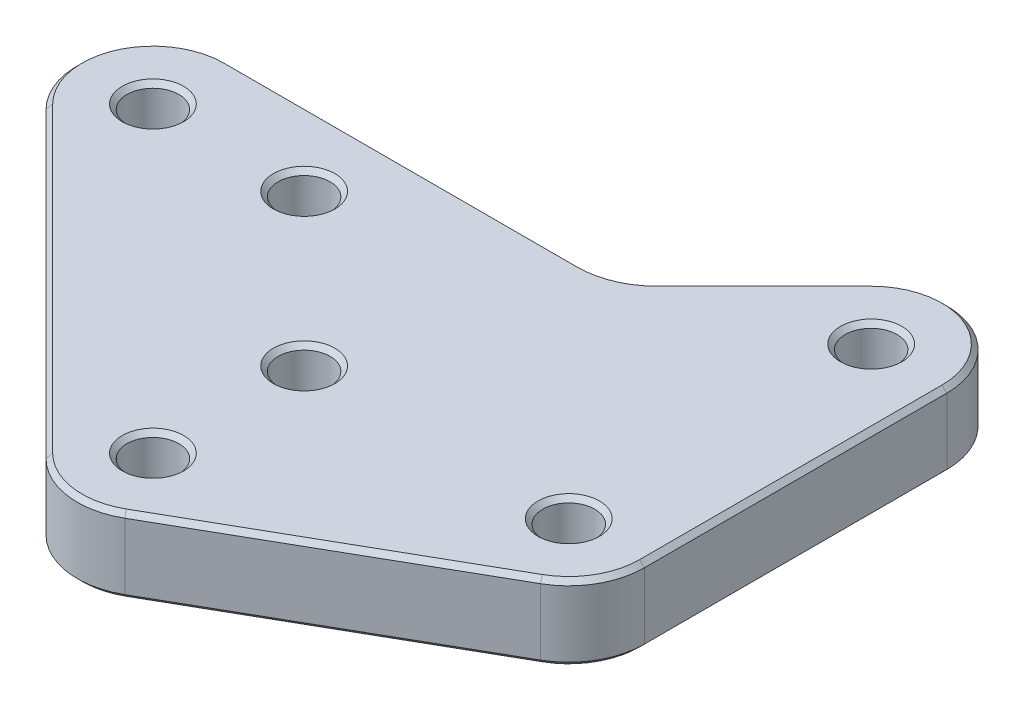
SolidWorks part; units mm, degrees
ref_plane "Front Plane" through (0, 0, 0) normal (0, 0, 1) x (1, 0, 0)
ref_plane "Top Plane" through (0, 0, 0) normal (0, 1, 0) x (1, 0, 0)
ref_plane "Right Plane" through (0, 0, 0) normal (1, 0, 0) x (0, 0, -1)
sketch "Sketch1" plane through (0, 0, 0) normal (0, 1, 0) x (1, 0, 0)
  line L15 (6.35, 25.4) -> (6.35, 0)
  line L16 (3.1505, -5.5133) -> (-19.0745, -18.2133)
  line L17 (-52.1151, 8.2099) -> (-26.7151, -17.1901)
  line L18 (-47.625, 19.05) -> (-17.9605, 19.05)
  line L19 (-13.4704, 20.9099) -> (-4.4901, 29.8901)
  circle A0 centre (0, 0) radius 2.1828
  circle A1 centre (0, 25.4) radius 2.1828
  circle A2 centre (-22.225, 0) radius 2.1828
  circle A3 centre (-22.225, -12.7) radius 2.1828
  circle A4 centre (-34.925, 12.7) radius 2.1828
  circle A5 centre (-47.625, 12.7) radius 2.1828
  arc A15 (3.1505, -5.5133) -> (6.35, 0) centre (0, 0) ccw
  arc A16 (-26.7151, -17.1901) -> (-19.0745, -18.2133) centre (-22.225, -12.7) ccw
  arc A17 (-47.625, 19.05) -> (-52.1151, 8.2099) centre (-47.625, 12.7) ccw
  arc A18 (6.35, 25.4) -> (-4.4901, 29.8901) centre (0, 25.4) ccw
  arc A19 (-17.9605, 19.05) -> (-13.4704, 20.9099) centre (-17.9605, 25.4) ccw
  point P18 (0, 0)
  point P25 (0, 0)
  point P26 (0, 0)
  point P27 (0, 0)
  point P28 (0, 0)
  point P31 (6.35, 19.05)
  point P32 (0, 0)
  dimension "D1" = 4.3656
  dimension "D2" = 4.3656
  dimension "D4" = 4.3656
  dimension "D7" = 4.3656
  dimension "D10" = 4.3656
  dimension "D12" = 4.3656
  dimension "D13" = 12.7
  dimension "D14" = 12.7
  dimension "D15" = 12.7
  dimension "D16" = 12.7
  dimension "D18" = 6.35
  dimension "D3" = 25.4
  dimension "D5" = 22.225
  dimension "D6" = 12.7
  dimension "D8" = 12.7
  dimension "D9" = 12.7
  dimension "D11" = 12.7
  dimension "D17" = 135
  dimension "D19" = 35.921
extrude "Boss-Extrude1" add sketch "Sketch1" along normal blind 6.35
chamfer "Chamfer1" distance 0.3969 angle 45 32 edges at (-47.625, 0, -10.5172) (-34.925, 0, -10.5172) (-22.225, 0, 14.8828) (-22.225, 0, 2.1828) (0, 0, -23.2172) (0, 0, 2.1828) (-39.4151, 0, 4.4901) (-23.0679, 0, 18.9938) (-7.962, 0, 11.8633) (5.4922, 0, 3.1872) (6.35, 0, -12.7) (-47.625, 6.35, -10.5172) (-22.225, 6.35, 14.8828) (0, 6.35, -23.2172) (6.35, 6.35, -12.7) (5.4922, 6.35, 3.1872) (-7.962, 6.35, 11.8633) (-23.0679, 6.35, 18.9938) (-39.4151, 6.35, 4.4901) (0, 6.35, 2.1828) (-22.225, 6.35, 2.1828) (-34.925, 6.35, -10.5172) (2.43, 0, -31.2666) (-8.9803, 0, -25.4) (-15.5305, 0, -19.5334) (-32.7928, 0, -19.05) (-53.4916, 0, -15.13) (-32.7928, 6.35, -19.05) (-15.5305, 6.35, -19.5334) (-8.9803, 6.35, -25.4) (2.43, 6.35, -31.2666) (-53.4916, 6.35, -15.13)
